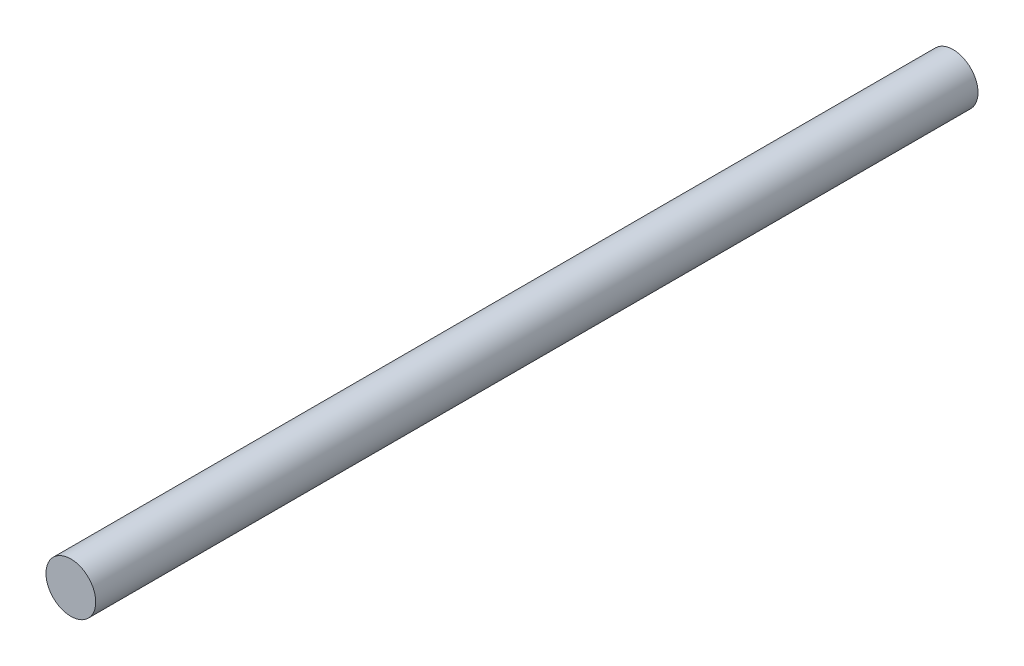
SolidWorks part; units mm, degrees
ref_plane "Front Plane" through (0, 0, 0) normal (0, 0, 1) x (1, 0, 0)
ref_plane "Top Plane" through (0, 0, 0) normal (0, 1, 0) x (1, 0, 0)
ref_plane "Right Plane" through (0, 0, 0) normal (1, 0, 0) x (0, 0, -1)
sketch "Sketch1" plane through (0, 0, 0) normal (0, 0, 1) x (1, 0, 0)
  circle A0 centre (0, 0) radius 2.794
  dimension "D1" = 5.588
extrude "Boss-Extrude1" add sketch "Sketch1" along normal blind 99.06
